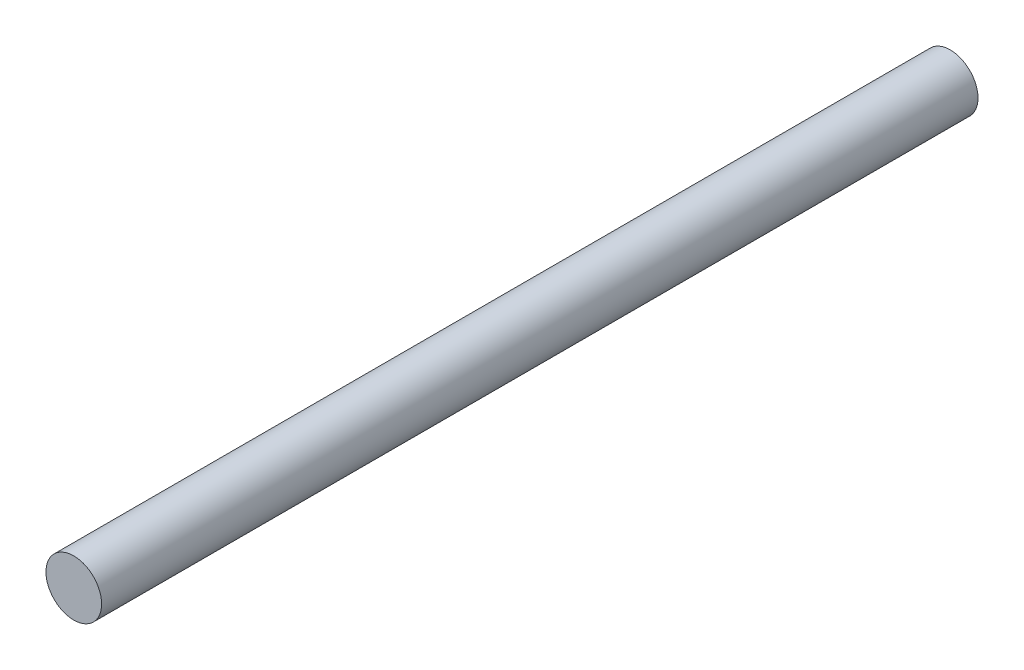
SolidWorks part; units mm, degrees
ref_plane "Front Plane" through (0, 0, 0) normal (0, 0, 1) x (1, 0, 0)
ref_plane "Top Plane" through (0, 0, 0) normal (0, 1, 0) x (1, 0, 0)
ref_plane "Right Plane" through (0, 0, 0) normal (1, 0, 0) x (0, 0, -1)
sketch "Sketch1" plane through (0, 0, 0) normal (0, 0, 1) x (1, 0, 0)
  circle A0 centre (0, 0) radius 6.35
  dimension "D1" = 12.7
extrude "Boss-Extrude1" add sketch "Sketch1" along normal blind 200
